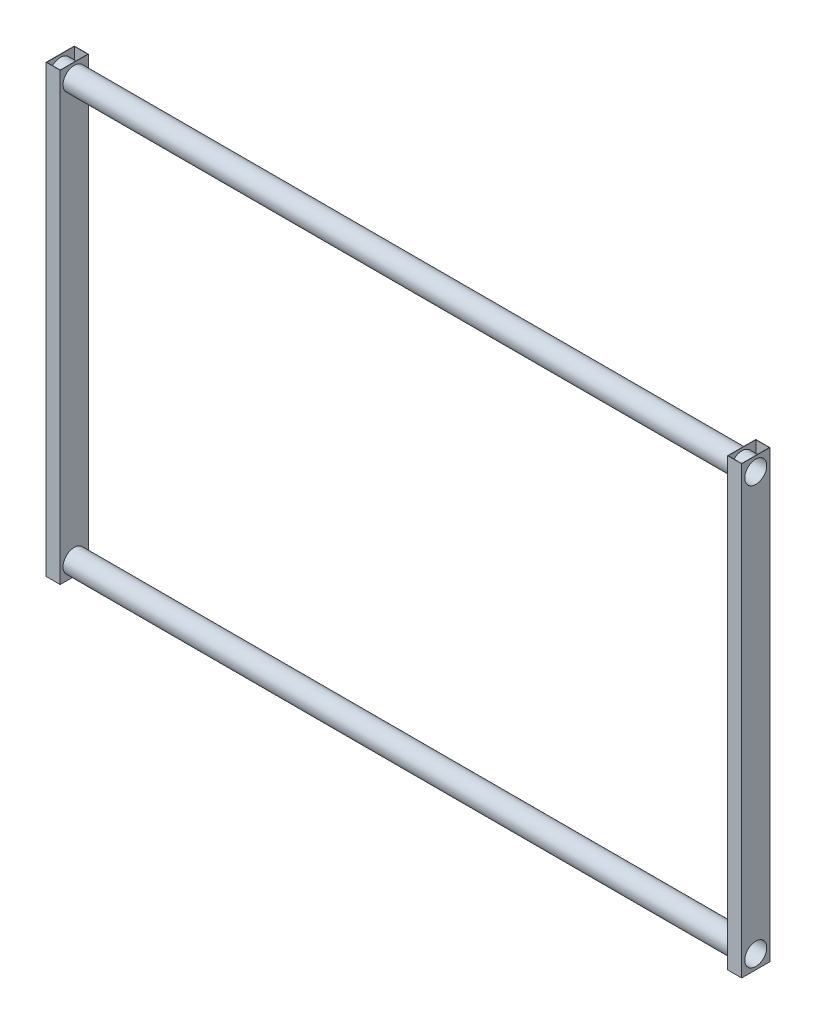
SolidWorks part; units mm, degrees
ref_plane "Front Plane" through (0, 0, 0) normal (0, 0, 1) x (1, 0, 0)
ref_plane "Top Plane" through (0, 0, 0) normal (0, 1, 0) x (1, 0, 0)
ref_plane "Right Plane" through (0, 0, 0) normal (1, 0, 0) x (0, 0, -1)
sketch "Sketch3" plane through (0, 0, 0) normal (0, 1, 0) x (1, 0, 0)
  line L0 (0, 209.8812) -> (0, -209.8812) construction
  line L2 (-209.8812, 0) -> (209.8812, 0) construction
  line L10 (2398, 209.8812) -> (2398, -209.8812) construction
  line L11 (1199, 209.8812) -> (1199, -209.8812) construction
  line L22 (-1, 49.5) -> (-49.5, 49.5)
  line L23 (0, 50.5) -> (-50.5, 50.5)
  line L24 (0, 50.5) -> (0, -50.5)
  line L25 (0, -50.5) -> (-50.5, -50.5)
  line L26 (-50.5, 50.5) -> (-50.5, -50.5)
  line L27 (-49.5, 49.5) -> (-49.5, -49.5)
  line L28 (-1, -49.5) -> (-49.5, -49.5)
  line L29 (-1, 49.5) -> (-1, -49.5)
  line L30 (2399, 49.5) -> (2399, -49.5)
  line L31 (2399, -49.5) -> (2447.5, -49.5)
  line L32 (2447.5, 49.5) -> (2447.5, -49.5)
  line L33 (2399, 49.5) -> (2447.5, 49.5)
  line L34 (2398, -50.5) -> (2448.5, -50.5)
  line L35 (2448.5, 50.5) -> (2448.5, -50.5)
  line L36 (2398, 50.5) -> (2448.5, 50.5)
  line L37 (2398, 50.5) -> (2398, -50.5)
  point P3 (0, 0)
  point P6 (0, 0)
  point P11 (0, 0)
  dimension "D1" = 101
  dimension "D2" = 50.5
  dimension "D3" = 1
  dimension "D7" = 2398
  dimension "D8" = 1199
extrude "Boss-Extrude1" add sketch "Sketch3" along normal blind 1600
sketch "Sketch8" plane through (-50.5, 0, 0) normal (-1, 0, 0) x (0, 0, 1)
  circle A0 centre (0, 50) radius 39.5
  circle A1 centre (0, 1550) radius 39.5
  dimension "D1" = 79
  dimension "D3" = 79
  dimension "D4" = 1500
  dimension "D2" = 50
extrude "Cut-Extrude1" cut sketch "Sketch8" against normal through all
sketch "Sketch9" plane through (0, 0, 0) normal (1, 0, 0) x (0, 0, -1)
  circle A0 centre (0, 50) radius 40.5
  circle A1 centre (0, 1550) radius 40.5
  dimension "D1" = 81
  dimension "D2" = 81
extrude "Cut-Extrude2" cut sketch "Sketch9" against normal up to surface (1 mm away) up to face at (-1, 50, 39.5)
sketch "Sketch10" plane through (2398, 0, 0) normal (-1, 0, 0) x (0, 0, 1)
  circle A0 centre (0, 50) radius 40.5
  circle A1 centre (0, 1550) radius 40.5
  dimension "D1" = 81
  dimension "D2" = 81
extrude "Cut-Extrude3" cut sketch "Sketch10" against normal up to surface (1 mm away) up to face at (2399, 50, -39.5)
sketch "Sketch13" plane through (2447.5, 0, 0) normal (-1, 0, 0) x (0, 0, 1)
  circle A0 centre (0, 50) radius 40.5
  circle A1 centre (0, 1550) radius 40.5
  circle A2 centre (0, 50) radius 39.5
  circle A3 centre (0, 1550) radius 39.5
  dimension "D1" = 81
  dimension "D2" = 81
  dimension "D3" = 79
  dimension "D4" = 79
extrude "Boss-Extrude2" add sketch "Sketch13" along normal up to surface (2497 mm away) up to face at (-49.5, 50, -39.5)
